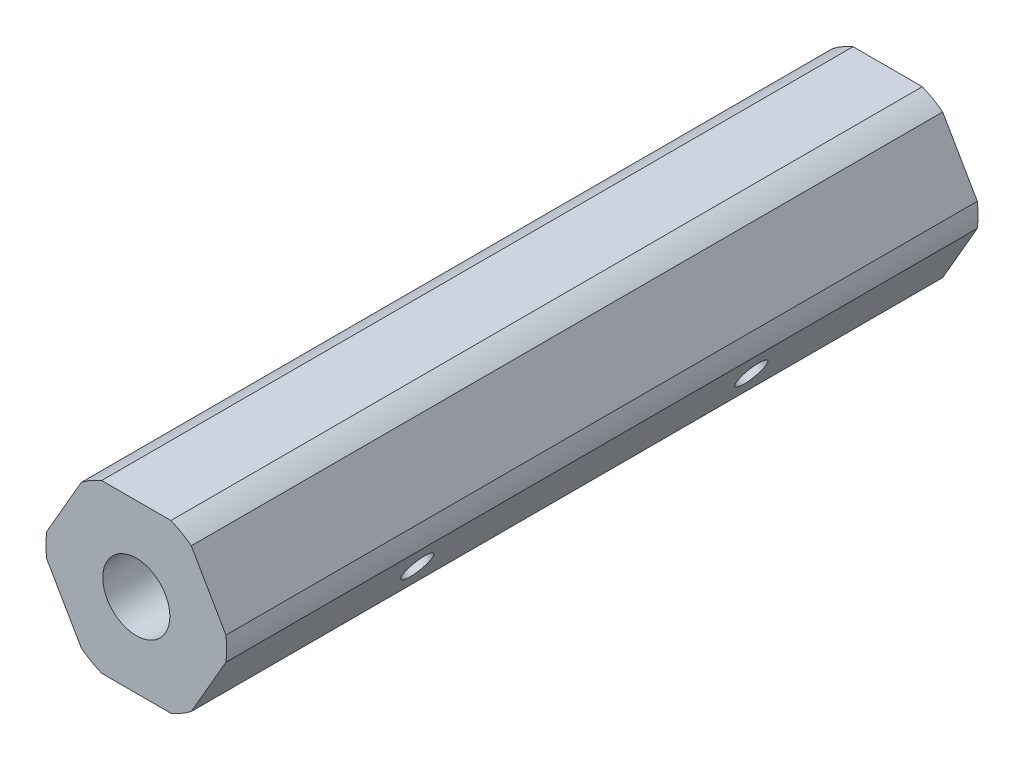
SolidWorks part; units mm, degrees
material "6061-T6 (SS)"
ref_plane "Front Plane" through (0, 0, 0) normal (0, 0, 1) x (1, 0, 0)
ref_plane "Top Plane" through (0, 0, 0) normal (0, 1, 0) x (1, 0, 0)
ref_plane "Right Plane" through (0, 0, 0) normal (1, 0, 0) x (0, 0, -1)
sketch "Sketch1" plane through (0, 0, 0) normal (0, 0, 1) x (1, 0, 0)
  line L1 (-2.635, -6.35) -> (2.635, -6.35)
  line L2 (4.1818, -5.457) -> (6.8168, -0.893)
  line L3 (6.8168, 0.893) -> (4.1818, 5.457)
  line L4 (2.635, 6.35) -> (-2.635, 6.35)
  line L5 (-4.1818, 5.457) -> (-6.8168, 0.893)
  line L6 (-6.8168, -0.893) -> (-4.1818, -5.457)
  circle A0 centre (0, 0) radius 6.35 construction
  arc A1 (-6.8168, 0.893) -> (-6.8168, -0.893) centre (0, 0) ccw
  arc A2 (-2.635, 6.35) -> (-4.1818, 5.457) centre (0, 0) ccw
  arc A3 (-4.1818, -5.457) -> (-2.635, -6.35) centre (0, 0) ccw
  arc A4 (2.635, -6.35) -> (4.1818, -5.457) centre (0, 0) ccw
  arc A5 (6.8168, -0.893) -> (6.8168, 0.893) centre (0, 0) ccw
  arc A6 (4.1818, 5.457) -> (2.635, 6.35) centre (0, 0) ccw
  dimension "D1" = 12.7
  dimension "D2" = 13.75
extrude "Boss-Extrude1" add sketch "Sketch1" along normal mid plane 57.15
hole_wizard "1/4-20 Tapped Hole1" positions "Sketch2" profile "Sketch3" tap size "1/4-20" standard "ANSI Inch" end condition through all
sketch "Sketch2" plane through (0, 0, 28.575) normal (0, 0, 1) x (1, 0, 0)
  point P0 (0, 0)
sketch "Sketch3" plane through (0, 0, 28.575) normal (1, 0, 0) x (0, -1, 0)
  line L0 (0, 0) -> (0, 57.15)
  line L1 (0, 57.15) -> (2.5527, 57.15)
  line L2 (2.5527, 57.15) -> (2.5527, 0)
  line L5 (2.5527, 0) -> (0, 0)
  line L11 (0, -6.35) -> (0, 107.95) construction
  dimension "Thru Tap Drill Dia." = 5.1054
  dimension "Thru Tap Drill Depth" = 57.15
cosmetic thread "Hole Thread1"
hole_wizard "#4-40 Tapped Hole1" positions "Sketch4" profile "Sketch5" tap size "#4-40" standard "ANSI Inch" end condition through all
sketch "Sketch4" plane through (0.7368, -11.4239, -31.75) normal (0.866, -0.5, 0) x (0, 0, -1)
  point P0 (-44.45, 120.65)
  point P3 (-19.05, 120.65)
  point P6 (-19.05, 9.525)
  point P9 (-44.45, 9.525)
sketch "Sketch5" plane through (61.0618, 93.0621, 12.7) normal (0, 0, 1) x (0.5, 0.866, 0)
  line L0 (0, 0) -> (0, 15.4789)
  line L1 (0, 15.4789) -> (1.1303, 15.4789)
  line L2 (1.1303, 15.4789) -> (1.1303, 0)
  line L3 (1.1303, 0) -> (0, 0)
  line L4 (0, -6.35) -> (0, 107.95) construction
  dimension "Thru Tap Drill Dia." = 2.2606
  dimension "Thru Tap Drill Depth" = 15.4789
cosmetic thread "Hole Thread2"
cosmetic thread "Hole Thread3"
hole_wizard "#4-40 Tapped Hole2" positions "Sketch6" profile "Sketch7" tap size "#4-40" standard "ANSI Inch" end condition through all
sketch "Sketch6" plane through (-54.8257, -107.661, -31.75) normal (0.866, -0.5, 0) x (0, 0, -1)
  point P0 (-44.45, 120.65)
  point P3 (-19.05, 120.65)
  point P6 (-19.05, 9.525)
  point P9 (-44.45, 9.525)
sketch "Sketch7" plane through (5.4993, -3.175, 12.7) normal (0, 0, 1) x (0.5, 0.866, 0)
  line L0 (0, 0) -> (0, 15.4789)
  line L1 (0, 15.4789) -> (1.1303, 15.4789)
  line L2 (1.1303, 15.4789) -> (1.1303, 0)
  line L3 (1.1303, 0) -> (0, 0)
  line L4 (0, -6.35) -> (0, 107.95) construction
  dimension "Thru Tap Drill Dia." = 2.2606
  dimension "Thru Tap Drill Depth" = 15.4789
